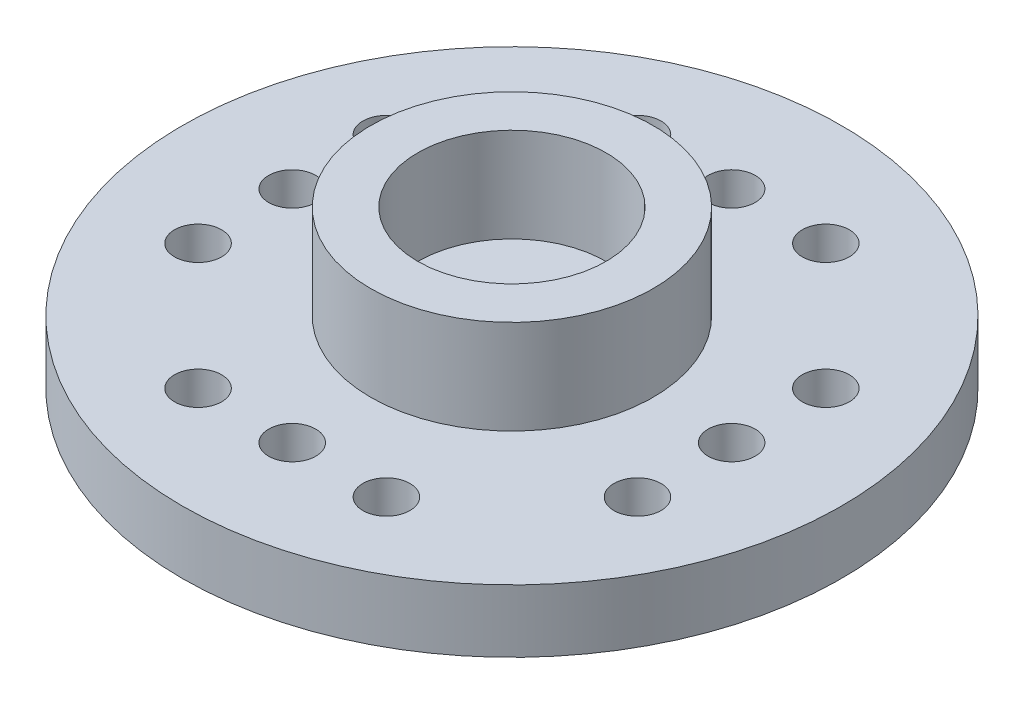
SolidWorks part; units mm, degrees
ref_plane "Front Plane" through (0, 0, 0) normal (0, 0, 1) x (1, 0, 0)
ref_plane "Top Plane" through (0, 0, 0) normal (0, 1, 0) x (1, 0, 0)
ref_plane "Right Plane" through (0, 0, 0) normal (1, 0, 0) x (0, 0, -1)
sketch "Sketch1" plane through (0, 0, 0) normal (0, 1, 0) x (1, 0, 0)
  circle A0 centre (0, 0) radius 10.5
  dimension "D1" = 21
extrude "Boss-Extrude1" add sketch "Sketch1" along normal blind 2
sketch "Sketch2" plane through (0, 2, 0) normal (0, 1, 0) x (1, 0, 0)
  circle A0 centre (0, 0) radius 4.5
  circle A1 centre (0, 0) radius 3
  dimension "D1" = 9
  dimension "D2" = 6
extrude "Boss-Extrude2" add sketch "Sketch2" along normal blind 3
sketch "Sketch3" plane through (0, 2, 0) normal (0, 1, 0) x (1, 0, 0)
  circle A0 centre (0, 0) radius 1
  dimension "D1" = 2
extrude "Cut-Extrude1" cut sketch "Sketch3" against normal blind 3
sketch "Sketch4" plane through (0, 0, 0) normal (0, -1, 0) x (1, 0, 0)
  circle A0 centre (0, 0) radius 4.25
  circle A1 centre (0, 0) radius 3.25
  circle A2 centre (0, 0) radius 2.75
  circle A3 centre (0, 0) radius 1 construction
  circle A4 centre (0, 0) radius 1
  circle M2 centre (0, 0) radius 1
  dimension "D1" = 8.5
  dimension "D2" = 6.5
  dimension "D3" = 5.5
extrude "Cut-Extrude2" cut sketch "Sketch4" against normal blind 0.5 contours A0 A1 | A2 M2
sketch "Sketch5" plane through (0, 0, 0) normal (0, -1, 0) x (1, 0, 0)
  line L0 (-5.3137, 7) -> (6.4564, 7) construction
  line L1 (7, 4.9566) -> (7, -5.128) construction
  circle A0 centre (0, 7) radius 0.75
  circle A1 centre (3, 7) radius 0.75
  circle A2 centre (-3, 7) radius 0.75
  dimension "D3" = 1.5
  dimension "D4" = 1.5
  dimension "D5" = 1.5
  dimension "D1" = 7
  dimension "D2" = 7
  dimension "D6" = 3
  dimension "D7" = 3
extrude "Cut-Extrude3" cut sketch "Sketch5" against normal blind 2.5
mirror "Mirror1" about plane through (0, 0, 0) normal (0, 0, 1) of "Cut-Extrude3"
sketch "Sketch7" plane through (0, 0, 0) normal (0, -1, 0) x (1, 0, 0)
  line L0 (7, 4.7852) -> (7, -3.6424) construction
  circle A0 centre (7, 0) radius 0.75
  circle A1 centre (7, 3) radius 0.75
  circle A2 centre (7, -3) radius 0.75
  dimension "D2" = 1.5
  dimension "D3" = 1.5
  dimension "D4" = 1.5
  dimension "D1" = 7
  dimension "D5" = 3
  dimension "D6" = 3
extrude "Cut-Extrude4" cut sketch "Sketch7" against normal blind 2.5
mirror "Mirror2" about plane through (0, 0, 0) normal (1, 0, 0) of "Cut-Extrude4"
